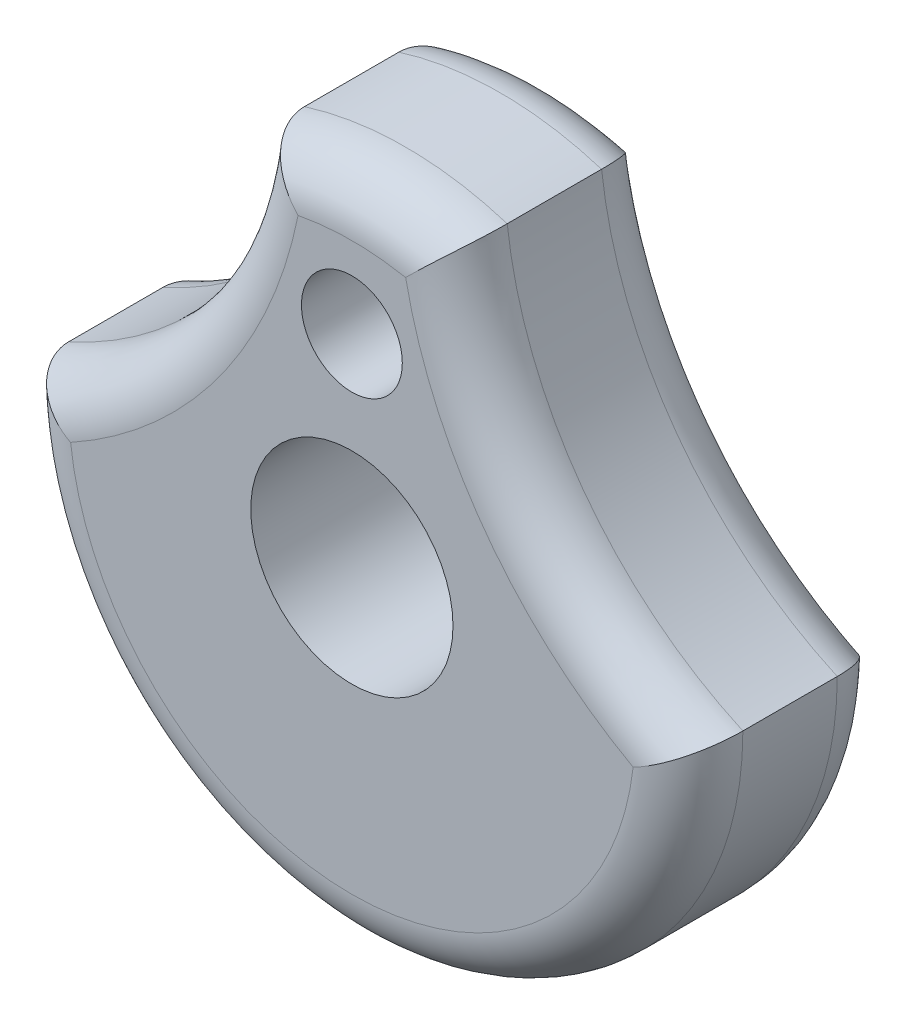
SolidWorks part; units mm, degrees
material "1023 Carbon Steel Sheet (SS)"
ref_plane "Front Plane" through (0, 0, 0) normal (0, 0, 1) x (1, 0, 0)
ref_plane "Top Plane" through (0, 0, 0) normal (0, 1, 0) x (1, 0, 0)
ref_plane "Right Plane" through (0, 0, 0) normal (1, 0, 0) x (0, 0, -1)
sketch "Sketch1" plane through (0, 0, 0) normal (0, 0, 1) x (1, 0, 0)
  circle A0 centre (0, 0) radius 15.875
  dimension "D1" = 31.75
extrude "Boss-Extrude1" add sketch "Sketch1" along normal blind 9.525
sketch "Sketch2" plane through (0, 0, 9.525) normal (0, 0, 1) x (1, 0, 0)
  circle A0 centre (0, 0) radius 4.7625
  dimension "D1" = 9.525
extrude "Cut-Extrude1" cut sketch "Sketch2" against normal blind 18.415
sketch "Sketch3" plane through (0, 0, 9.525) normal (0, 0, 1) x (1, 0, 0)
  line L0 (0, 19.5645) -> (0, -18.4868) construction
  circle A0 centre (0, 9.525) radius 2.3749
  dimension "D2" = 4.7498
  dimension "D1" = 38.0512
  dimension "D3" = 9.525
extrude "Cut-Extrude2" cut sketch "Sketch3" against normal blind 18.415
sketch "Sketch4" plane through (0, 0, 9.525) normal (0, 0, 1) x (1, 0, 0)
  line L0 (0, 23.3779) -> (0, -3.6476) construction
  line L1 (-18.6526, 0) -> (19.7303, 0) construction
  arc A0 (15.875, 0) -> (4.7752, 15.1398) centre (23.694, 17.3714) cw
  circle A1 centre (0, 0) radius 15.875 construction
  arc A2 (-15.875, 0) -> (-4.7752, 15.1398) centre (-23.694, 17.3714) ccw
  spline S0 degree 2 poles (-15.875, 0) (-15.4208, 10.9941) (-4.7752, 15.1398) knots 0 0 0 1 1 1
  spline S1 degree 2 poles (15.875, 0) (15.3439, 11.113) (4.7752, 15.1398) knots 0 0 0 1 1 1
  dimension "D3" = 19.05
  dimension "D1" = 27.0255
  dimension "D2" = 38.3828
  dimension "D4" = 4.7752
extrude "Cut-Extrude4" cut sketch "Sketch4" against normal blind 18.415 contours S0 A2 | S1 A0
fillet "Fillet1" radius 2.54 4 edges at (8.3307, 6.1077, 9.525) (0, -15.875, 9.525) (0, 15.875, 9.525) (-8.3307, 6.1077, 9.525)
fillet "Fillet2" radius 2.54 4 edges at (-8.3307, 6.1077, 0) (0, -15.875, 0) (0, 15.875, 0) (8.3307, 6.1077, 0)
